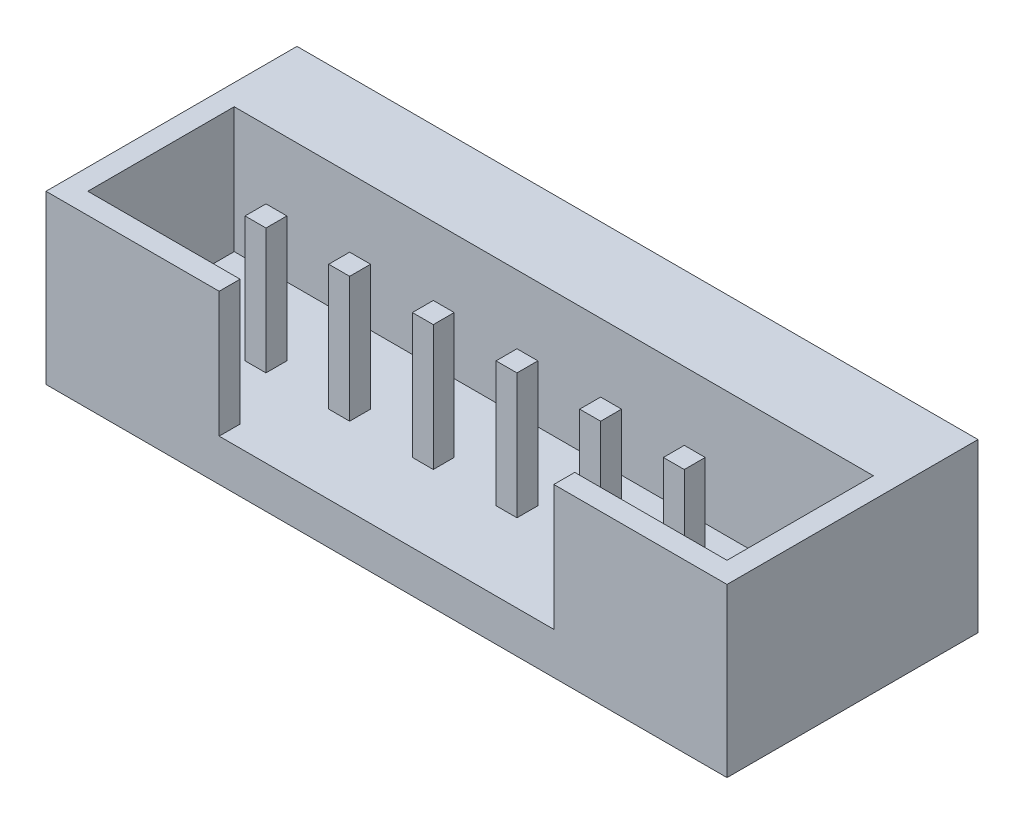
SolidWorks part; units mm, degrees
ref_plane "Front Plane" through (0, 0, 0) normal (0, 0, 1) x (1, 0, 0)
ref_plane "Top Plane" through (0, 0, 0) normal (0, 1, 0) x (1, 0, 0)
ref_plane "Right Plane" through (0, 0, 0) normal (1, 0, 0) x (0, 0, -1)
sketch "Sketch1" plane through (0, 0, 0) normal (0, 1, 0) x (1, 0, 0)
  line L1 (-8.14, -3) -> (8.14, -3)
  line L2 (-8.14, -3) -> (-8.14, 3)
  line L3 (-8.14, 3) -> (8.14, 3)
  line L4 (8.14, -3) -> (8.14, 3)
  line L5 (-8.14, -3) -> (8.14, 3) construction
  line L6 (-8.14, 3) -> (8.14, -3) construction
  point P0 (0, 0)
  dimension "D1" = 16.28
  dimension "D2" = 6
extrude "Boss-Extrude1" add sketch "Sketch1" along normal blind 4
sketch "Sketch2" plane through (0, 4, 0) normal (0, 1, 0) x (1, 0, 0)
  line L8 (-8.14, 3) -> (-8.14, -3) construction
  line L10 (-7.64, -2.5) -> (-7.64, 1)
  line L11 (-7.64, 1) -> (7.64, 1)
  line L12 (7.64, -2.5) -> (7.64, 1)
  line L13 (8.14, -3) -> (8.14, 3) construction
  line L14 (8.14, 3) -> (-8.14, 3) construction
  line L16 (-4, -3) -> (4, -3)
  line L17 (-8.14, -3) -> (8.14, -3) construction
  line L18 (-7.64, -2.5) -> (-4, -2.5)
  line L19 (-4, -2.5) -> (-4, -3)
  line L20 (7.64, -2.5) -> (4, -2.5)
  line L21 (4, -2.5) -> (4, -3)
  dimension "D1" = 0.5
  dimension "D2" = 0.5
  dimension "D3" = 2
  dimension "D4" = 8
extrude "Cut-Extrude1" cut sketch "Sketch2" against normal blind 3
sketch "Sketch4" plane through (0, 1, 0) normal (0, 1, 0) x (1, 0, 0)
  line L0 (-3.25, -0.6314) -> (-3.25, -1.1314)
  line L1 (-5.25, -0.6314) -> (-4.75, -0.6314)
  line L2 (-5.25, -0.6314) -> (-5.25, -1.1314)
  line L3 (-5.25, -1.1314) -> (-4.75, -1.1314)
  line L4 (-4.75, -0.6314) -> (-4.75, -1.1314)
  line L5 (-5.25, -0.6314) -> (-4.75, -1.1314) construction
  line L6 (-5.25, -1.1314) -> (-4.75, -0.6314) construction
  line L7 (-3.25, -0.6314) -> (-2.75, -0.6314)
  line L8 (-2.75, -0.6314) -> (-2.75, -1.1314)
  line L9 (-3.25, -1.1314) -> (-2.75, -1.1314)
  line L10 (-1.25, -0.6314) -> (-1.25, -1.1314)
  line L11 (-1.25, -0.6314) -> (-0.75, -0.6314)
  line L12 (-0.75, -0.6314) -> (-0.75, -1.1314)
  line L13 (-1.25, -1.1314) -> (-0.75, -1.1314)
  line L14 (0.75, -0.6314) -> (0.75, -1.1314)
  line L15 (0.75, -0.6314) -> (1.25, -0.6314)
  line L16 (1.25, -0.6314) -> (1.25, -1.1314)
  line L17 (0.75, -1.1314) -> (1.25, -1.1314)
  line L18 (2.75, -0.6314) -> (2.75, -1.1314)
  line L19 (2.75, -0.6314) -> (3.25, -0.6314)
  line L20 (3.25, -0.6314) -> (3.25, -1.1314)
  line L21 (2.75, -1.1314) -> (3.25, -1.1314)
  line L22 (4.75, -0.6314) -> (4.75, -1.1314)
  line L23 (4.75, -0.6314) -> (5.25, -0.6314)
  line L24 (5.25, -0.6314) -> (5.25, -1.1314)
  line L25 (4.75, -1.1314) -> (5.25, -1.1314)
  line L26 (-7.64, 1) -> (-7.64, -2.5) construction
  point P0 (-5, -0.8814)
  dimension "D1" = 0.5
  dimension "D2" = 0.5
  dimension "D4" = 2.39
  dimension "D3" = 6
extrude "Boss-Extrude2" add sketch "Sketch4" along normal blind 3
